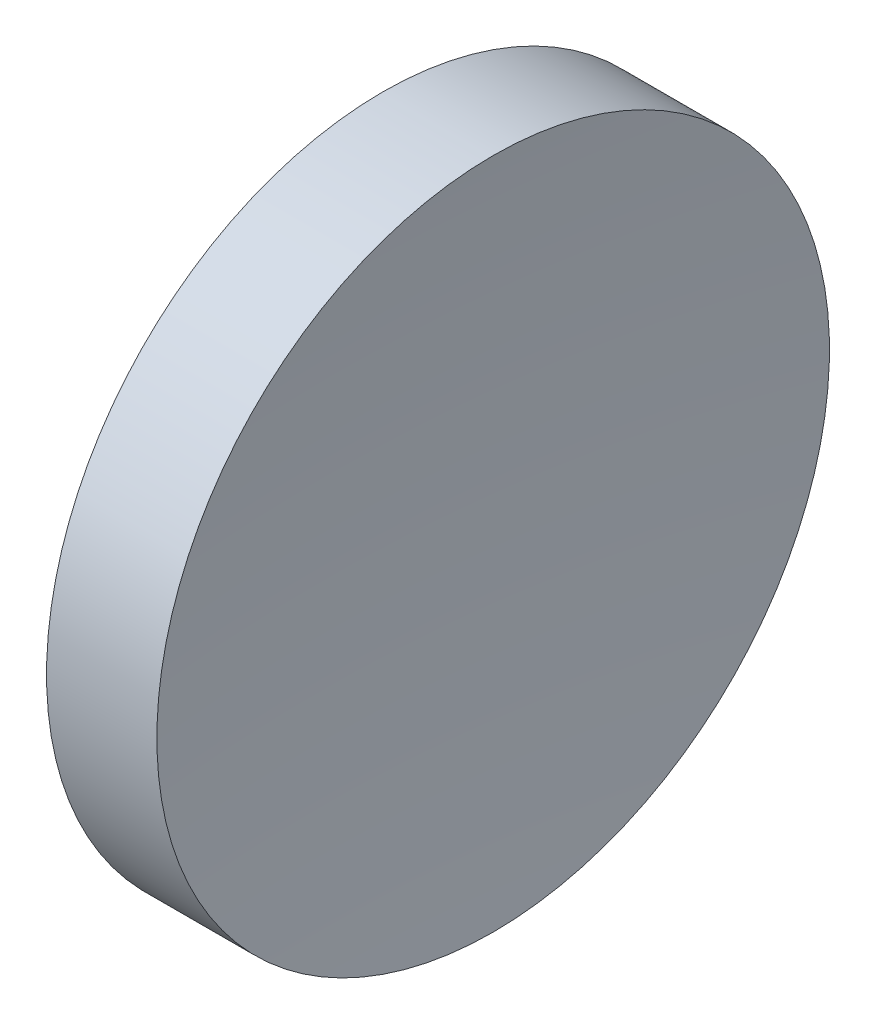
SolidWorks part; units mm, degrees
ref_plane "前视基准面" through (0, 0, 0) normal (0, 0, 1) x (1, 0, 0)
ref_plane "上视基准面" through (0, 0, 0) normal (0, 1, 0) x (1, 0, 0)
ref_plane "右视基准面" through (0, 0, 0) normal (1, 0, 0) x (0, 0, -1)
sketch "草图1" plane through (0, 0, 0) normal (0, 0, 1) x (1, 0, 0)
  line L0 (57.9722, 32.6084) -> (67.9741, 32.6084) construction
  line L1 (64.1952, 38.8584) -> (62.145, 38.8584)
  line L2 (61.3061, 32.6084) -> (63.9061, 32.6084)
  arc A0 (62.145, 38.8584) -> (61.3061, 32.6084) centre (85.0061, 32.6084) ccw
  arc A1 (64.1952, 38.8584) -> (63.9061, 32.6084) centre (131.6061, 32.6084) ccw
revolve "旋转1" add sketch "草图1" angle 360 about L0
